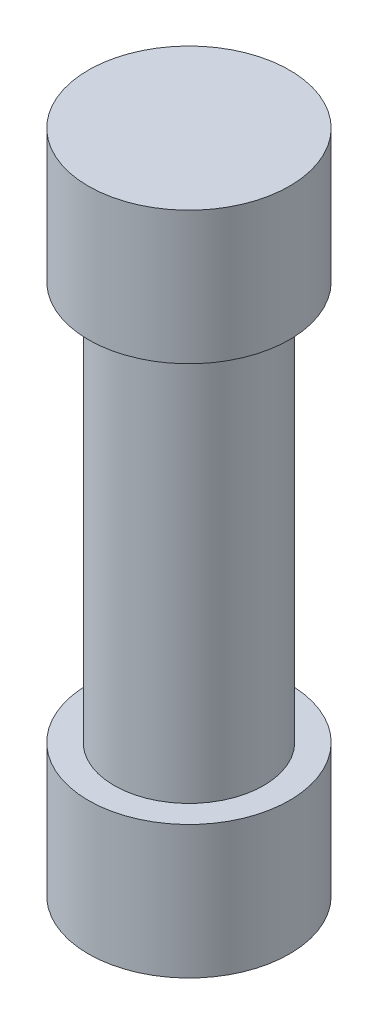
SolidWorks part; units mm, degrees
ref_plane "Front Plane" through (0, 0, 0) normal (0, 0, 1) x (1, 0, 0)
ref_plane "Top Plane" through (0, 0, 0) normal (0, 1, 0) x (1, 0, 0)
ref_plane "Right Plane" through (0, 0, 0) normal (1, 0, 0) x (0, 0, -1)
sketch "Sketch1" plane through (0, 0, 0) normal (0, 1, 0) x (1, 0, 0)
  circle A0 centre (0, 0) radius 3.025
  dimension "D1" = 6.05
extrude "Boss-Extrude1" add sketch "Sketch1" along normal blind 4 contours A0
sketch "Sketch2" plane through (0, 4, 0) normal (0, 1, 0) x (1, 0, 0)
  circle A0 centre (0, 0) radius 2.25
  dimension "D1" = 4.5
extrude "Boss-Extrude2" add sketch "Sketch2" along normal blind 12
sketch "Sketch3" plane through (0, 16, 0) normal (0, 1, 0) x (1, 0, 0)
  circle A0 centre (0, 0) radius 3.025
  dimension "D1" = 6.05
extrude "Boss-Extrude3" add sketch "Sketch3" along normal blind 4
